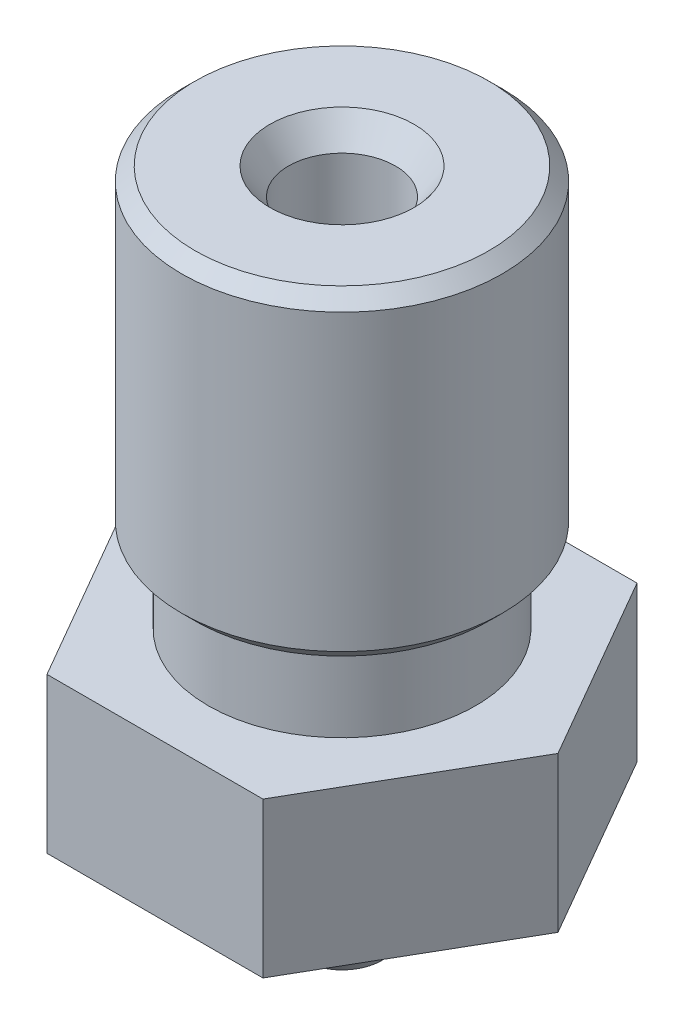
SolidWorks part; units mm, degrees
material "Brass"
ref_plane "Front Plane" through (0, 0, 0) normal (0, 0, 1) x (1, 0, 0)
ref_plane "Top Plane" through (0, 0, 0) normal (0, 1, 0) x (1, 0, 0)
ref_plane "Right Plane" through (0, 0, 0) normal (1, 0, 0) x (0, 0, -1)
sketch "Sketch1" plane through (0, 0, 0) normal (0, 0, 1) x (1, 0, 0)
  line L0 (0, -6.25) -> (0, 6.25) construction
  line L1 (0.3, -6.25) -> (0.3, -5.05)
  line L2 (0.3, -5.05) -> (0.995, -4.7406)
  line L3 (0.995, -4.7406) -> (0.995, -4.1522)
  line L4 (0.995, -4.1522) -> (1, -4.15)
  line L5 (1, -4.15) -> (1, 5.75)
  line L6 (1, 5.75) -> (1.3501, 6.25)
  line L7 (1.3501, 6.25) -> (3, 6.25)
  line L8 (2.5, 0.25) -> (3, 0.25)
  line L9 (3, 6.25) -> (3, 0.25)
  line L11 (2.5, 0.25) -> (2.5, -1.25)
  line L12 (2.5, -1.25) -> (3.5, -1.25)
  line L13 (3.5, -1.25) -> (3.5, -4.15)
  line L14 (3.5, -4.15) -> (2.2204, -4.15)
  line L15 (2.2204, -4.15) -> (0.75, -6.25)
  line L16 (0.75, -6.25) -> (0.3, -6.25)
  dimension "D1" = 12.5
  dimension "D2" = 125
  dimension "A" = 0.6
  dimension "D4" = 2
  dimension "D5" = 7
  dimension "D" = 1.99
  dimension "D6" = 6
  dimension "D7" = 125
  dimension "D8" = 0.5
  dimension "C" = 1.2
  dimension "B" = 1.5
  dimension "D11" = 7.5
  dimension "E" = 10.4
  dimension "D13" = 114
  dimension "D14" = 6
  dimension "D15" = 5
revolve "Revolve1" add sketch "Sketch1" angle 360 about L0
sketch "Sketch2" plane through (0, -4.15, 0) normal (0, -1, 0) x (1, 0, 0)
  line L1 (2.0207, 3.5) -> (-2.0207, 3.5)
  line L2 (-2.0207, 3.5) -> (-4.0415, 0)
  line L3 (-4.0415, 0) -> (-2.0207, -3.5)
  line L4 (-2.0207, -3.5) -> (2.0207, -3.5)
  line L5 (2.0207, -3.5) -> (4.0415, 0)
  line L6 (4.0415, 0) -> (2.0207, 3.5)
  circle A0 centre (0, 0) radius 3.5 construction
  circle A1 centre (0, 0) radius 1.6225
  dimension "D1" = 7
extrude "Boss-Extrude1" add sketch "Sketch2" against normal up to surface (2.9 mm away) up to face at (0, -1.25, -2.5)
chamfer "Chamfer1" distance 0.25 angle 45 2 edges at (0, 0.25, -3) (0, 6.25, -3)
